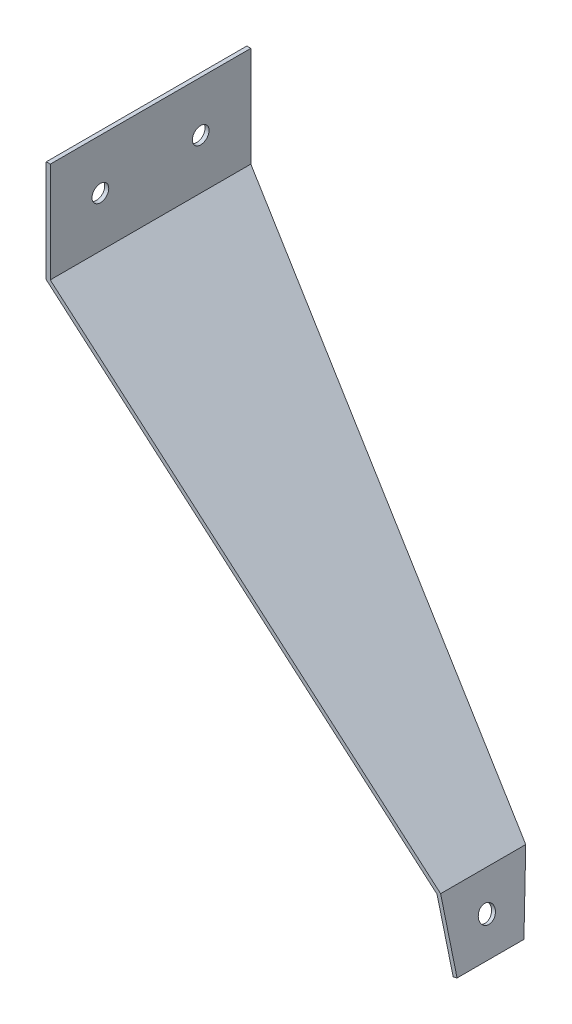
SolidWorks part; units mm, degrees
material "6061-T6 (SS)"
ref_plane "Front Plane" through (0, 0, 0) normal (0, 0, 1) x (1, 0, 0)
ref_plane "Top Plane" through (0, 0, 0) normal (0, 1, 0) x (1, 0, 0)
ref_plane "Right Plane" through (0, 0, 0) normal (1, 0, 0) x (0, 0, -1)
sketch "Sketch1" plane through (0, 0, 0) normal (0, 0, 1) x (1, 0, 0)
  line L0 (0, 0) -> (0, 38.1)
  line L1 (0, 0) -> (148.2978, -127.7815)
  line L2 (148.2978, -127.7815) -> (154.5501, -152.4)
  line L3 (148.2978, -127.7815) -> (135.8788, -78.8819) construction
  line L4 (-1.524, -0.6985) -> (-1.524, 38.1)
  line L5 (-1.524, -0.6985) -> (146.9389, -128.6224)
  line L6 (146.9389, -128.6224) -> (153.073, -152.7751)
  line L7 (153.073, -152.7751) -> (154.5501, -152.4)
  line L8 (-1.524, 38.1) -> (0, 38.1)
  dimension "D1" = 130.75
  dimension "D2" = 35
  dimension "D3" = 190.5
  dimension "D4" = 25.4
  dimension "D5" = 38.1
  dimension "D6" = 1.524
extrude "Boss-Extrude1" add sketch "Sketch1" against normal blind 76.2
sketch "Sketch2" plane through (108.8262, 27.6383, 0) normal (0.9692, 0.2462, 0) x (0, 0, -1)
  line L0 (0, -185.7538) -> (25.4, -185.7538) construction
  line L1 (76.2, -185.7538) -> (0, -185.7538) construction
  line L2 (25.4, -185.7538) -> (76.2, 0)
  line L3 (76.2, 0) -> (76.2, -185.7538)
  line L4 (76.2, -185.7538) -> (25.4, -185.7538)
  dimension "D1" = 25.4
extrude "Cut-Extrude1" cut sketch "Sketch2" against normal through all
sketch "Sketch3" plane through (108.8262, 27.6383, 0) normal (0.9692, 0.2462, 0) x (0, 0, -1)
  line L0 (0, -185.7538) -> (12.7, -185.7538) construction
  line L1 (25.4, -185.7538) -> (0, -185.7538) construction
  line L2 (12.7, -185.7538) -> (16.1732, -160.3538) construction
  line L3 (32.3464, -160.3538) -> (0, -160.3538) construction
  circle A0 centre (14.4366, -173.0538) radius 3.175
  dimension "D1" = 6.35
extrude "Cut-Extrude2" cut sketch "Sketch3" against normal through all
sketch "Sketch4" plane through (0, 0, 0) normal (1, 0, 0) x (0, 0, -1)
  line L0 (0, 38.1) -> (76.2, 38.1) construction
  line L1 (38.1, 38.1) -> (38.1, 0) construction
  line L2 (76.2, 0) -> (0, 0) construction
  line L3 (38.1, 19.05) -> (0, 19.05) construction
  line L4 (0, 0) -> (0, 38.1) construction
  line L5 (38.1, 19.05) -> (76.2, 19.05) construction
  line L6 (76.2, 0) -> (76.2, 38.1) construction
  circle A0 centre (19.05, 19.05) radius 3.175
  circle A1 centre (57.15, 19.05) radius 3.175
  dimension "D1" = 6.35
  dimension "D2" = 6.35
extrude "Cut-Extrude3" cut sketch "Sketch4" against normal through all
